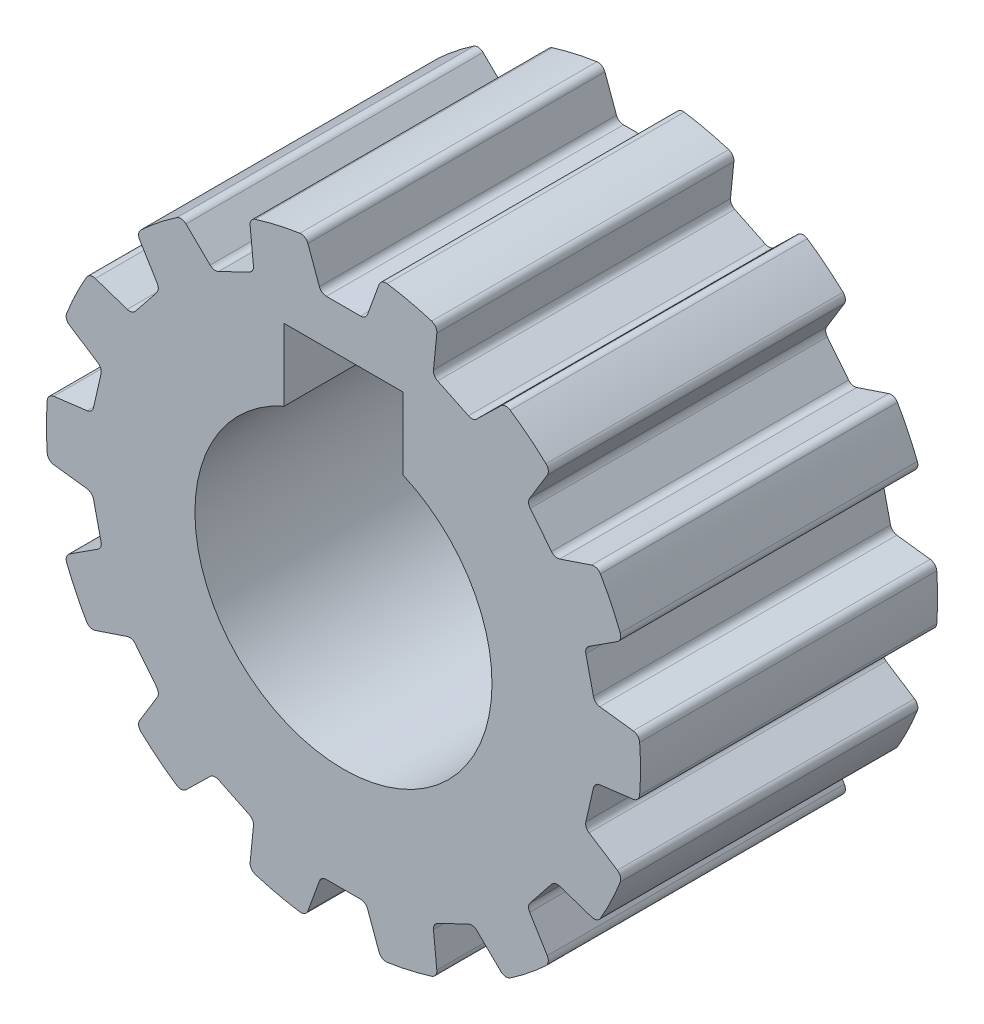
SolidWorks part; units mm, degrees
ref_plane "Front Plane" through (0, 0, 0) normal (0, 0, 1) x (1, 0, 0)
ref_plane "Top Plane" through (0, 0, 0) normal (0, 1, 0) x (1, 0, 0)
ref_plane "Right Plane" through (0, 0, 0) normal (1, 0, 0) x (0, 0, -1)
sketch "Sketch2" plane through (0, 0, 0) normal (0, 0, 1) x (1, 0, 0)
  line L0 (0, 0) -> (0, 6.6707) construction
  line L3 (2, 4.5826) -> (2, 7)
  line L4 (2, 7) -> (-2, 7)
  line L5 (-2, 4.5826) -> (-2, 7)
  line L6 (0, 5) -> (-2, 7) construction
  line L7 (2, 7) -> (0, 5) construction
  circle A0 centre (0, 0) radius 10
  arc A1 (-2, 4.5826) -> (2, 4.5826) centre (0, 0) ccw
  point P4 (0, 5)
  dimension "D1" = 20
  dimension "D2" = 10
  dimension "D3" = 4
  dimension "D4" = 7
extrude "Boss-Extrude1" add sketch "Sketch2" along normal blind 10
sketch "Sketch3" plane through (0, 0, 10) normal (0, 0, 1) x (1, 0, 0)
  line L0 (0, 0) -> (0, 10) construction
  line L1 (-0.75, 8.5) -> (0.75, 8.5)
  line L2 (0.75, 8.5) -> (1.2666, 9.9195)
  line L3 (-0.75, 8.5) -> (-1.2666, 9.9195)
  circle A0 centre (0, 0) radius 10 construction
  circle M5 centre (0, 0) radius 10
  dimension "D1" = 1.5
  dimension "D2" = 0.75
  dimension "D3" = 110
  dimension "D4" = 110
  dimension "D5" = 8.5
extrude "Cut-Extrude1" cut sketch "Sketch3" against normal through all and the other way through all contours L1 L0 L3 M5 | L0 L1 L2 M5
pattern_circular "CirPattern1" count 14 over 360 about axis through (0, 0, 0) along (0, 0, 1) of "Cut-Extrude1"
fillet "Fillet1" radius 0.25 56 edges at (4.3637, 7.3328, 5) (3.0123, 7.9836, 5) (0.75, 8.5, 5) (-0.75, 8.5, 5) (-3.0123, 7.9836, 5) (-4.3637, 7.3328, 5) (-6.178, 5.886, 5) (-7.1132, 4.7133, 5) (-8.12, 2.6226, 5) (-8.4538, 1.1602, 5) (-8.4538, -1.1602, 5) (-8.12, -2.6226, 5) (-7.1132, -4.7133, 5) (-6.178, -5.886, 5) (-4.3637, -7.3328, 5) (-3.0123, -7.9836, 5) (-0.75, -8.5, 5) (0.75, -8.5, 5) (3.0123, -7.9836, 5) (4.3637, -7.3328, 5) (6.178, -5.886, 5) (7.1132, -4.7133, 5) (8.12, -2.6226, 5) (8.4538, -1.1602, 5) (8.4538, 1.1602, 5) (8.12, 2.6226, 5) (7.1132, 4.7133, 5) (6.178, 5.886, 5)
